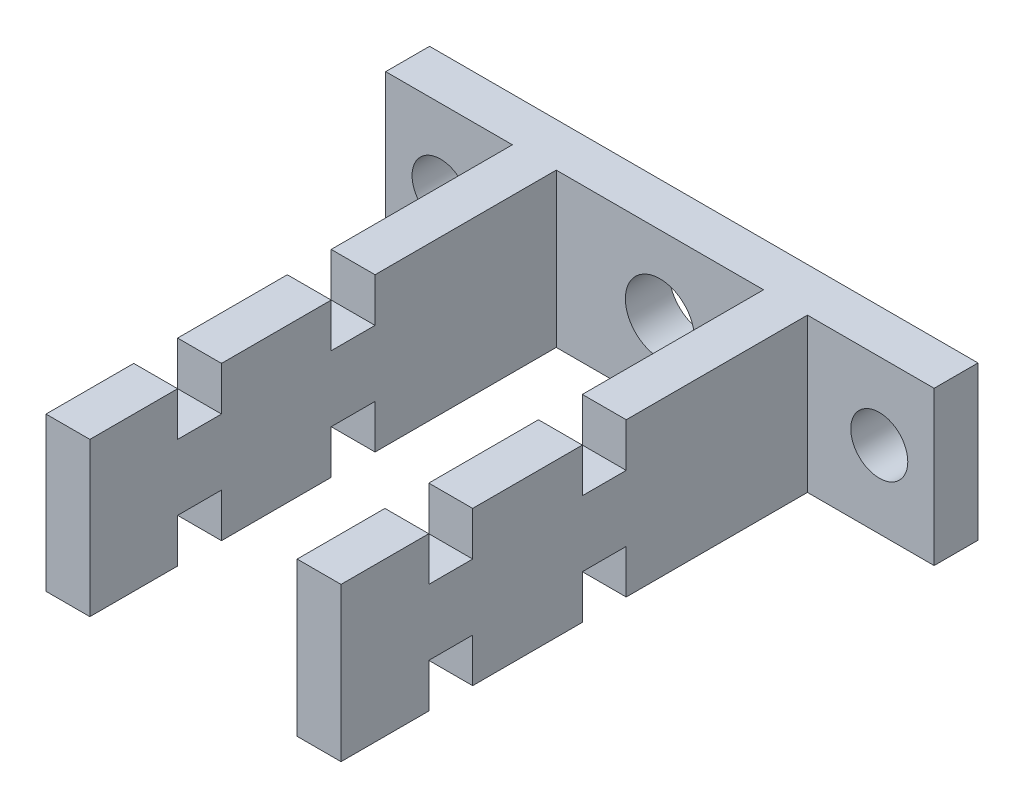
SolidWorks part; units mm, degrees
ref_plane "Front Plane" through (0, 0, 0) normal (0, 0, 1) x (1, 0, 0)
ref_plane "Top Plane" through (0, 0, 0) normal (0, 1, 0) x (1, 0, 0)
ref_plane "Right Plane" through (0, 0, 0) normal (1, 0, 0) x (0, 0, -1)
sketch "Sketch1" plane through (0, 0, 0) normal (0, 0, 1) x (1, 0, 0)
  line L1 (30.2, 25) -> (4.8, 25) construction
  line L2 (1.625, 20.555) -> (33.375, 20.555)
  line L3 (1.625, 20.555) -> (1.625, 29.445)
  line L4 (1.625, 29.445) -> (33.375, 29.445)
  line L5 (33.375, 20.555) -> (33.375, 29.445)
  line L6 (1.625, 20.555) -> (33.375, 29.445) construction
  line L7 (1.625, 29.445) -> (33.375, 20.555) construction
  circle A2 centre (17.5, 25) radius 2
  circle A3 centre (17.5, 25) radius 2 construction
  point P11 (17.5, 25)
  dimension "D1" = 31.75
  dimension "D2" = 8.89
  dimension "D3" = 25.4
extrude "Boss-Extrude1" add sketch "Sketch1" along normal blind 2.54
sketch "Sketch3" plane through (0, 0, 2.54) normal (0, 0, 1) x (1, 0, 0)
  line L0 (33.375, 29.445) -> (1.625, 29.445) construction
  line L1 (11.5, 29.445) -> (8.96, 29.445)
  line L2 (11.5, 29.445) -> (11.5, 20.555)
  line L3 (11.5, 20.555) -> (8.96, 20.555)
  line L4 (8.96, 29.445) -> (8.96, 20.555)
  line L5 (1.625, 20.555) -> (33.375, 20.555) construction
  line L6 (17.5, 29.445) -> (17.5, 20.555) construction
  line L7 (23.5, 20.555) -> (26.04, 20.555)
  line L8 (26.04, 29.445) -> (26.04, 20.555)
  line L9 (23.5, 29.445) -> (26.04, 29.445)
  line L10 (23.5, 29.445) -> (23.5, 20.555)
  dimension "D1" = 6
  dimension "D2" = 2.54
extrude "Boss-Extrude2" add sketch "Sketch3" along normal blind 27
sketch "Sketch4" plane through (0, 29.445, 0) normal (0, 1, 0) x (1, 0, 0)
  line L0 (8.96, -29.54) -> (8.96, -2.54) construction
  line L1 (8.96, -24.46) -> (26.04, -24.46)
  line L2 (8.96, -24.46) -> (8.96, -21.92)
  line L3 (8.96, -21.92) -> (26.04, -21.92)
  line L4 (26.04, -24.46) -> (26.04, -21.92)
  line L5 (26.04, -29.54) -> (26.04, -2.54) construction
  line L6 (26.04, -29.54) -> (23.5, -29.54) construction
  line L7 (8.96, -15.57) -> (8.96, -13.03)
  line L8 (8.96, -15.57) -> (26.04, -15.57)
  line L9 (26.04, -15.57) -> (26.04, -13.03)
  line L10 (8.96, -13.03) -> (26.04, -13.03)
  dimension "D1" = 5.08
  dimension "D2" = 2.54
  dimension "D4" = 6.35
  dimension "D3" = 2
extrude "Cut-Extrude1" cut sketch "Sketch4" against normal blind 2.54
ref_plane "Plane1" through (0, 25, 0) normal (0, 1, 0) x (1, 0, 0)
mirror "Mirror1" about plane through (0, 25, 0) normal (0, 1, 0) of "Cut-Extrude1"
hole_wizard "Tap Drill for M4x0.7 Tap1" positions "Sketch8" profile "Sketch7" hole size "M4x0.7" standard "ANSI Metric" end condition through all
sketch "Sketch8" plane through (0, 0, 2.54) normal (0, 0, 1) x (1, 0, 0)
  point P0 (4.8, 25)
  point P3 (30.2, 25)
sketch "Sketch7" plane through (4.8, 25, 2.54) normal (1, 0, 0) x (0, -1, 0)
  line L0 (0, 0) -> (0, 2.54)
  line L1 (0, 2.54) -> (1.65, 2.54)
  line L2 (1.65, 2.54) -> (1.65, 0)
  line L5 (1.65, 0) -> (0, 0)
  line L11 (0, -6.35) -> (0, 107.95) construction
  dimension "Thru Hole Dia." = 3.3
  dimension "Thru Hole Depth" = 2.54
